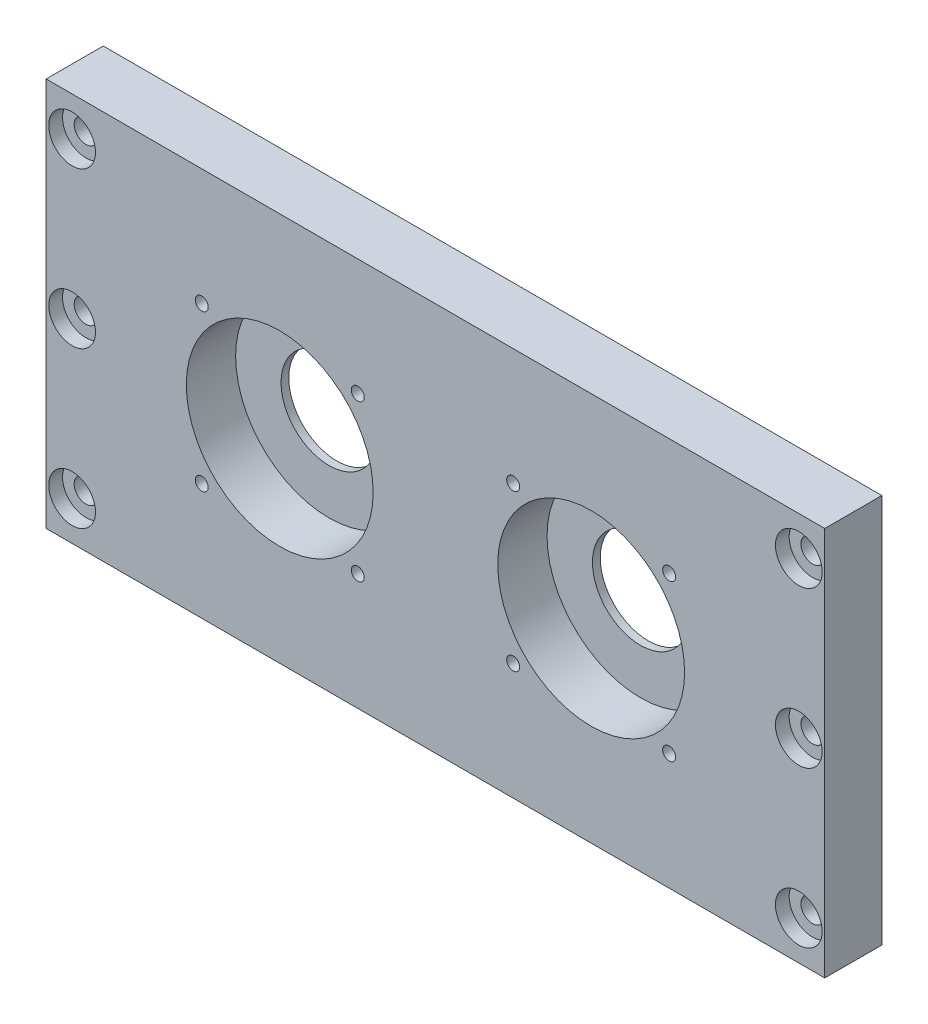
SolidWorks part; units mm, degrees
ref_plane "Front Plane" through (0, 0, 0) normal (0, 0, 1) x (1, 0, 0)
ref_plane "Top Plane" through (0, 0, 0) normal (0, 1, 0) x (1, 0, 0)
ref_plane "Right Plane" through (0, 0, 0) normal (1, 0, 0) x (0, 0, -1)
sketch "Sketch1" plane through (0, 0, 0) normal (0, 0, 1) x (1, 0, 0)
  line L1 (-150, -75) -> (150, -75)
  line L2 (-150, -75) -> (-150, 75)
  line L3 (-150, 75) -> (150, 75)
  line L4 (150, -75) -> (150, 75)
  line L5 (-150, -75) -> (150, 75) construction
  line L6 (-150, 75) -> (150, -75) construction
  point P0 (0, 0)
  dimension "D1" = 300
  dimension "D2" = 150
extrude "Boss-Extrude1" add sketch "Sketch1" along normal blind 22
sketch "Sketch2" plane through (0, 0, 0) normal (0, 0, 1) x (1, 0, 0)
  line L0 (12.1, 0) -> (-12.1, 0) construction
  line L1 (-150, 75) -> (-150, -75) construction
  circle A0 centre (-60, 0) radius 36
  circle A1 centre (-60, 0) radius 18.5
  dimension "D1" = 72
  dimension "D3" = 37
  dimension "D4" = 90
  dimension "D2" = 60
extrude "Cut-Extrude2" cut sketch "Sketch2" against normal blind 19 from surface at 22 contours A0 starting at face at (0, 0, 22)
sketch "Sketch4" plane through (0, 0, 0) normal (0, 0, 1) x (1, 0, 0)
  circle A0 centre (-60, 0) radius 18.5
  dimension "D1" = 37
extrude "Cut-Extrude4" cut sketch "Sketch4" against normal up to next from surface
sketch "Sketch8" plane through (0, 0, 0) normal (0, 0, 1) x (1, 0, 0)
sketch "Sketch12" plane through (0, 0, 22) normal (0, 0, 1) x (1, 0, 0)
  line L0 (12.1, 0) -> (-12.1, 0) construction
  line L1 (0, -12.1) -> (0, 12.1) construction
  point P0 (-140, 60)
  point P1 (-140, 0)
  point P2 (-140, -60)
  dimension "D1" = 60
  dimension "D2" = 140
hole_wizard "CBORE for M8 Hex Head Bolt1" positions "3DSketch5" profile "Sketch13" counterbore size "M8" standard "ISO" end condition through all
sketch3d "3DSketch5"
  point P0 (-140, 60, 22)
  point P3 (-140, 0, 22)
  point P6 (-140, -60, 22)
sketch "Sketch13" plane through (-140, 60, 22) normal (1, 0, 0) x (0, -1, 0)
  line L0 (0, 0) -> (0, 22)
  line L1 (0, 22) -> (4.5, 22)
  line L3 (4.5, 22) -> (4.5, 5.3)
  line L4 (4.5, 5.3) -> (9.0055, 5.3)
  line L5 (9.0055, 5.3) -> (9.0055, 0)
  line L7 (9.0055, 0) -> (0, 0)
  line L11 (0, -6.35) -> (0, 107.95) construction
  dimension "Thru Hole Dia." = 9
  dimension "Thru Hole Depth" = 22
  dimension "C'Bore Dia." = 18.011
  dimension "C'Bore Depth" = 5.3
mirror "Mirror1" about plane through (0, 0, 0) normal (1, 0, 0) of "Cut-Extrude2", "Cut-Extrude4", "CBORE for M8 Hex Head Bolt1"
sketch "Sketch14" plane through (0, 0, 22) normal (0, 0, 1) x (1, 0, 0)
  line L0 (-60, 0) -> (-29.948, 30.052) construction
  line L1 (12.1, 0) -> (-12.1, 0) construction
  circle A0 centre (-60, 0) radius 42.5 construction
  dimension "D1" = 85
  dimension "D2" = 45
hole_wizard "Tap Drill for M6 Tap1" positions "3DSketch6" profile "Sketch15" hole size "M6" standard "ISO" end condition through all
sketch3d "3DSketch6"
  point P0 (-29.948, 30.052, 22)
sketch "Sketch15" plane through (-29.948, 30.052, 22) normal (1, 0, 0) x (0, -1, 0)
  line L0 (0, 0) -> (0, 22)
  line L1 (0, 22) -> (2.5, 22)
  line L2 (2.5, 22) -> (2.5, 0)
  line L5 (2.5, 0) -> (0, 0)
  line L11 (0, -6.35) -> (0, 107.95) construction
  dimension "Thru Hole Dia." = 5
  dimension "Thru Hole Depth" = 22
pattern_circular "CirPattern1" count 4 over 360 about axis through (-60, 0, 0) along (0, 0, 1) of "Tap Drill for M6 Tap1"
mirror "Mirror2" about plane through (0, 0, 0) normal (1, 0, 0) of "CirPattern1", "Tap Drill for M6 Tap1"
